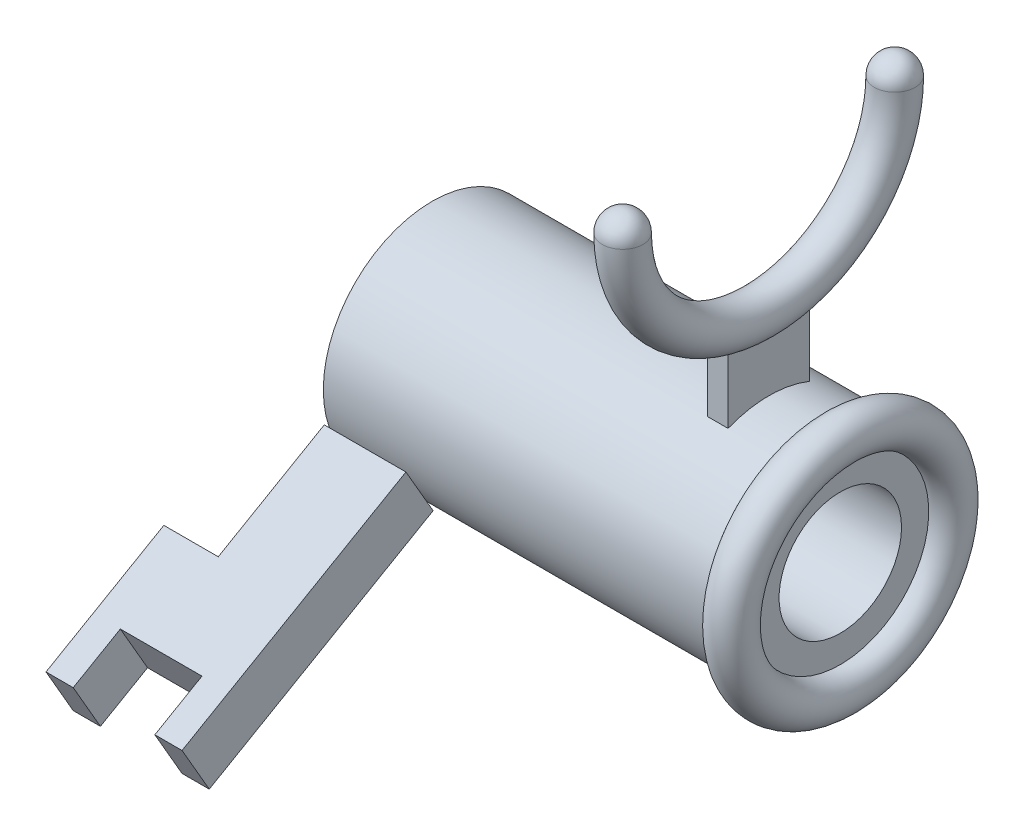
SolidWorks part; units mm, degrees
ref_plane "Front Plane" through (0, 0, 0) normal (0, 0, 1) x (1, 0, 0)
ref_plane "Top Plane" through (0, 0, 0) normal (0, 1, 0) x (1, 0, 0)
ref_plane "Right Plane" through (0, 0, 0) normal (1, 0, 0) x (0, 0, -1)
sketch "Sketch2" plane through (0, 0, 0) normal (1, 0, 0) x (0, 0, -1)
  circle A0 centre (0, 0) radius 40
  dimension "D1" = 80
extrude "Boss-Extrude1" add sketch "Sketch2" along normal blind 150
sketch "Sketch3" plane through (150, 0, 0) normal (1, 0, 0) x (0, 0, -1)
  circle A0 centre (0, 0) radius 22.5
  dimension "D1" = 45
extrude "Cut-Extrude1" cut sketch "Sketch3" against normal up to next
sketch "Sketch4" plane through (0, 0, 0) normal (0, 1, 0) x (1, 0, 0)
  line L0 (-12.4065, 0) -> (167.2061, 0) construction
  circle A0 centre (150, 40) radius 7.5
  point P7 (150, 40)
  dimension "D1" = 7.5
revolve "Revolve1" add sketch "Sketch4" angle 360 about L0
sketch "Sketch9" plane through (0, 0, 0) normal (1, 0, 0) x (0, 0, -1)
  point P0 (0, 115)
  dimension "D1" = 115
ref_plane "Plane1" through (0, 115, 0) normal (0, 1, 0) x (1, 0, 0)
sketch "Sketch10" plane through (0, 115, 0) normal (0, 1, 0) x (1, 0, 0)
  line L0 (150, 47.5) -> (150, -47.5) construction
  line L1 (142.5, 40) -> (157.5, 40) construction
  line L2 (157.5, -40) -> (157.5, 40) construction
  line L3 (-32.4114, 0) -> (193.6054, 0) construction
  circle A0 centre (120, 50) radius 7.5
  arc A1 (157.5, 40) -> (142.5, 40) centre (150, 40) ccw construction
  arc A2 (142.5, -40) -> (157.5, -40) centre (150, -40) ccw construction
  point P15 (150, 40)
  dimension "D1" = 7.5
  dimension "D2" = 30
  dimension "D3" = 50
other "AlignGroup1"
revolve "Revolve4" add sketch "Sketch10" angle 180 about L3
sketch "Sketch12" plane through (0, 115, 0) normal (0, 1, 0) x (1, 0, 0)
  line L0 (112.5, 50) -> (127.5, 50) construction
  arc A0 (112.5, 50) -> (127.5, 50) centre (120, 50) cw
  circle A1 centre (120, 50) radius 7.5 construction
revolve "Revolve-Thin1" add sketch "Sketch12" angle 180 about L0
sketch "Sketch13" plane through (0, 115, 0) normal (0, 1, 0) x (1, 0, 0)
  line L0 (112.5, -50) -> (127.5, -50)
  arc A0 (112.5, -50) -> (127.5, -50) centre (120, -50) cw
  circle A1 centre (120, -50) radius 7.5 construction
revolve "Revolve5" add sketch "Sketch13" angle 180 about L0
sketch "Sketch14" plane through (0, 0, 0) normal (0, 1, 0) x (1, 0, 0)
  line L0 (142.5, 0) -> (0, 0) construction
  line L1 (123.75, -15) -> (116.25, -15)
  line L2 (123.75, -15) -> (123.75, 15)
  line L3 (123.75, 15) -> (116.25, 15)
  line L4 (116.25, -15) -> (116.25, 15)
  line L5 (123.75, -15) -> (116.25, 15) construction
  line L6 (123.75, 15) -> (116.25, -15) construction
  line L7 (127.5, -50) -> (127.5, 50) construction
  line L10 (112.5, 50) -> (127.5, 50) construction
  line L11 (124.5, 50) -> (111, 50) construction
  circle A0 centre (120, 50) radius 7.5 construction
  point P0 (120, 0)
  point P9 (120, 50)
  dimension "D1" = 30
  dimension "D2" = 7.5
extrude "Boss-Extrude2" add sketch "Sketch14" along normal up to next from surface
ref_plane "Plane2" through (0, 0, 0) normal (0, 0.866, 0.5) x (-1, 0, 0)
sketch "Sketch15" plane through (0, 0, 0) normal (0, 0.866, 0.5) x (-1, 0, 0)
  line L0 (0, 40) -> (0, 85)
  line L1 (0, 85) -> (20, 85)
  line L2 (20, 85) -> (20, 135)
  line L3 (20, 135) -> (10, 135)
  line L4 (10, 135) -> (10, 115)
  line L5 (10, 115) -> (-20, 115)
  line L6 (-20, 115) -> (-20, 135)
  line L7 (-20, 135) -> (-30, 135)
  line L8 (-30, 135) -> (-30, 40)
  line L9 (0, 40) -> (-142.5, 40) construction
  line L10 (-142.5, 0) -> (0, 0) construction
  line L11 (0, 40) -> (-30, 40)
  dimension "D1" = 85
  dimension "D2" = 115
  dimension "D3" = 135
  dimension "D4" = 10
  dimension "D5" = 50
  dimension "D6" = 30
  dimension "D7" = 40
extrude "Boss-Extrude3" add sketch "Sketch15" along normal mid plane 20 separate body
